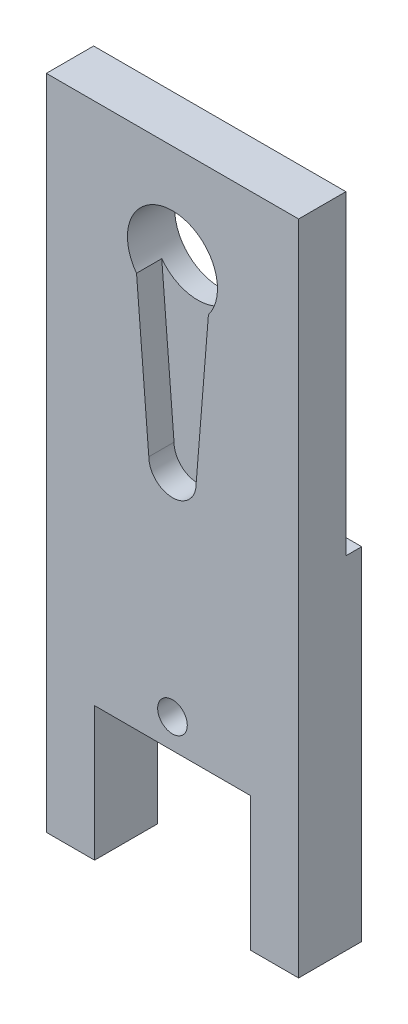
SolidWorks part; units mm, degrees
ref_plane "Front Plane" through (0, 0, 0) normal (0, 0, 1) x (1, 0, 0)
ref_plane "Top Plane" through (0, 0, 0) normal (0, 1, 0) x (1, 0, 0)
ref_plane "Right Plane" through (0, 0, 0) normal (1, 0, 0) x (0, 0, -1)
sketch "Sketch3" plane through (0, 0, 0) normal (0, 0, 1) x (1, 0, 0)
  line L1 (-10, 35) -> (10, 35)
  line L2 (-10, 35) -> (-10, -35)
  line L3 (-10, -35) -> (10, -35)
  line L4 (10, 35) -> (10, -35)
  line L5 (-10, 35) -> (10, -35) construction
  line L6 (-10, -35) -> (10, 35) construction
  point P0 (0, 0)
  dimension "D1" = 20
  dimension "D2" = 70
extrude "Boss-Extrude3" add sketch "Sketch3" along normal blind 5
sketch "Sketch4" plane through (0, 0, 5) normal (0, 0, 1) x (1, 0, 0)
  line L0 (-1.875, 12.7392) -> (1.875, 12.7392)
  line L1 (-2.85, 24.85) -> (2.85, 24.85)
  line L2 (-2.85, 24.85) -> (-1.875, 12.7392)
  line L3 (2.85, 24.85) -> (1.875, 12.7392)
  line L4 (10, -35) -> (10, 35) construction
  line L7 (10, 35) -> (-10, 35) construction
  circle A0 centre (0, 27) radius 3.57
  arc A1 (-1.875, 12.7392) -> (1.875, 12.7392) centre (0, 12.7392) ccw
  dimension "D1" = 7.14
  dimension "D2" = 3.75
  dimension "D3" = 5.7
  dimension "D4" = 12.15
  dimension "D5" = 12.15
  dimension "D6" = 10
  dimension "D7" = 8
extrude "Cut-Extrude2" cut sketch "Sketch4" against normal blind 2 contours L0 A1 | A0 L2 L0 L3
sketch "Sketch6" plane through (0, 0, 3) normal (0, 0, 1) x (1, 0, 0)
  line L0 (10, 35) -> (-10, 35) construction
  line L1 (-10, 35) -> (-10, -35) construction
  circle A0 centre (0, 27) radius 3.57
  dimension "D1" = 7.14
  dimension "D2" = 8
  dimension "D3" = 10
extrude "Cut-Extrude3" cut sketch "Sketch6" against normal blind 3
sketch "Sketch7" plane through (0, 0, 5) normal (0, 0, 1) x (1, 0, 0)
  line L0 (10, -35) -> (10, 35) construction
  line L1 (-6.175, -6.5) -> (6.175, -6.5)
  line L2 (-6.175, -6.5) -> (-6.175, -29.5)
  line L3 (-6.175, -29.5) -> (6.175, -29.5)
  line L4 (6.175, -6.5) -> (6.175, -29.5)
  line L5 (-6.175, -6.5) -> (6.175, -29.5) construction
  line L6 (-6.175, -29.5) -> (6.175, -6.5) construction
  line L7 (-10, -35) -> (10, -35) construction
  line L8 (0, -18) -> (16.5777, -18) construction
  circle A0 centre (0, -4.18) radius 1.175
  circle A1 centre (0, -31.82) radius 1.175
  point P0 (0, -18)
  dimension "D6" = 2.35
  dimension "D1" = 12.35
  dimension "D2" = 23
  dimension "D3" = 10
  dimension "D4" = 17
  dimension "D5" = 10
  dimension "D7" = 2.32
extrude "Cut-Extrude4" cut sketch "Sketch7" against normal blind 5
sketch "Sketch8" plane through (10, 0, 0) normal (1, 0, 0) x (0, 0, -1)
  line L6 (0, 35) -> (-1.25, 35)
  line L7 (0, 35) -> (0, 10)
  line L8 (0, 10) -> (-1.25, 10)
  line L9 (-1.25, 35) -> (-1.25, 10)
  dimension "D1" = 25
  dimension "D2" = 1.25
extrude "Cut-Extrude5" cut sketch "Sketch8" against normal blind 30
sketch "Sketch10" plane through (0, 0, 5) normal (0, 0, 1) x (1, 0, 0)
  line L0 (-10, 35) -> (-10, -35) construction
  line L1 (-10, -17.1147) -> (10, -17.1147)
  line L2 (-10, -17.1147) -> (-10, -35)
  line L3 (-10, -35) -> (10, -35)
  line L4 (10, -17.1147) -> (10, -35)
extrude "Cut-Extrude6" cut sketch "Sketch10" against normal blind 10
